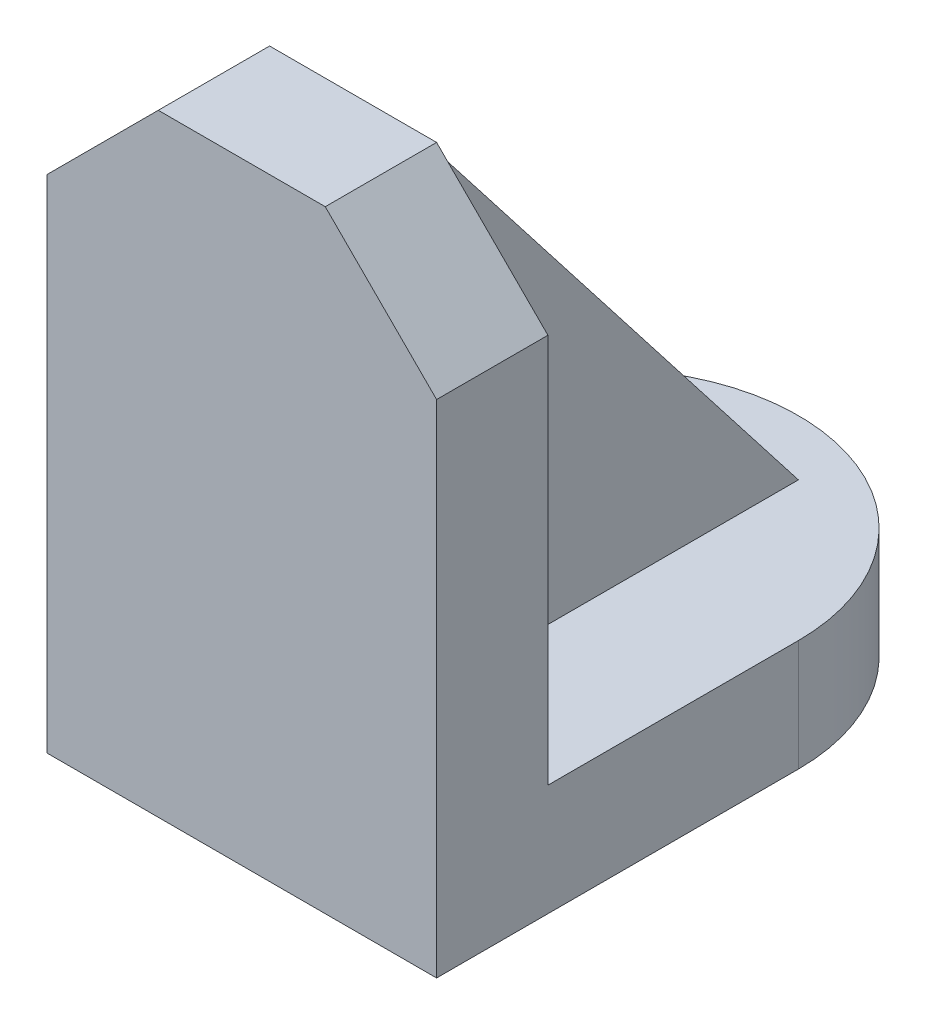
SolidWorks part; units mm, degrees
ref_plane "Front Plane" through (0, 0, 0) normal (0, 0, 1) x (1, 0, 0)
ref_plane "Top Plane" through (0, 0, 0) normal (0, 1, 0) x (1, 0, 0)
ref_plane "Right Plane" through (0, 0, 0) normal (1, 0, 0) x (0, 0, -1)
sketch "Sketch1" plane through (0, 0, 0) normal (0, 1, 0) x (1, 0, 0)
  line L0 (-21, 19.5) -> (21, 19.5) construction
  line L2 (-21, 19.5) -> (-21, -19.5)
  line L3 (-21, -19.5) -> (21, -19.5)
  line L4 (21, 19.5) -> (21, -19.5)
  line L5 (-21, 19.5) -> (21, -19.5) construction
  line L6 (-21, -19.5) -> (21, 19.5) construction
  arc A0 (-1.5534, -1.4425) -> (1.5534, -1.4425) centre (0, 19.5) ccw
  arc A1 (21, 19.5) -> (-21, 19.5) centre (0, 19.5) ccw
  point P0 (0, 0)
  dimension "D1" = 42
  dimension "D2" = 39
extrude "Boss-Extrude3" add sketch "Sketch1" along normal blind 12
sketch "Sketch4" plane through (0, 12, 0) normal (0, 1, 0) x (1, 0, 0)
  line L0 (21, 19.5) -> (21, -19.5) construction
  line L1 (-21, -19.5) -> (21, -19.5)
  line L2 (-21, -19.5) -> (-21, -7.5)
  line L3 (-21, -7.5) -> (21, -7.5)
  line L4 (21, -19.5) -> (21, -7.5)
  dimension "D1" = 12
extrude "Boss-Extrude4" add sketch "Sketch4" along normal blind 54 contours L2 L1 L4 L3
chamfer "Chamfer1" distance 12 angle 45 1 edges at (-21, 66, 13.5)
chamfer "Chamfer2" distance 12 angle 45 1 edges at (21, 66, 13.5)
ref_plane "Plane3" through (-6, 0, 0) normal (-1, 0, 0) x (0, 0, 1)
sketch "Sketch7" plane through (-6, 0, 0) normal (-1, 0, 0) x (0, 0, 1)
  line L0 (7.5, 12) -> (-34.5, 12)
  line L1 (-19.5, 12) -> (-40.5, 12) construction
  line L2 (-34.5, 12) -> (7.5, 66)
  line L3 (7.5, 66) -> (7.5, 12)
extrude "Boss-Extrude6" add sketch "Sketch7" against normal blind 12
